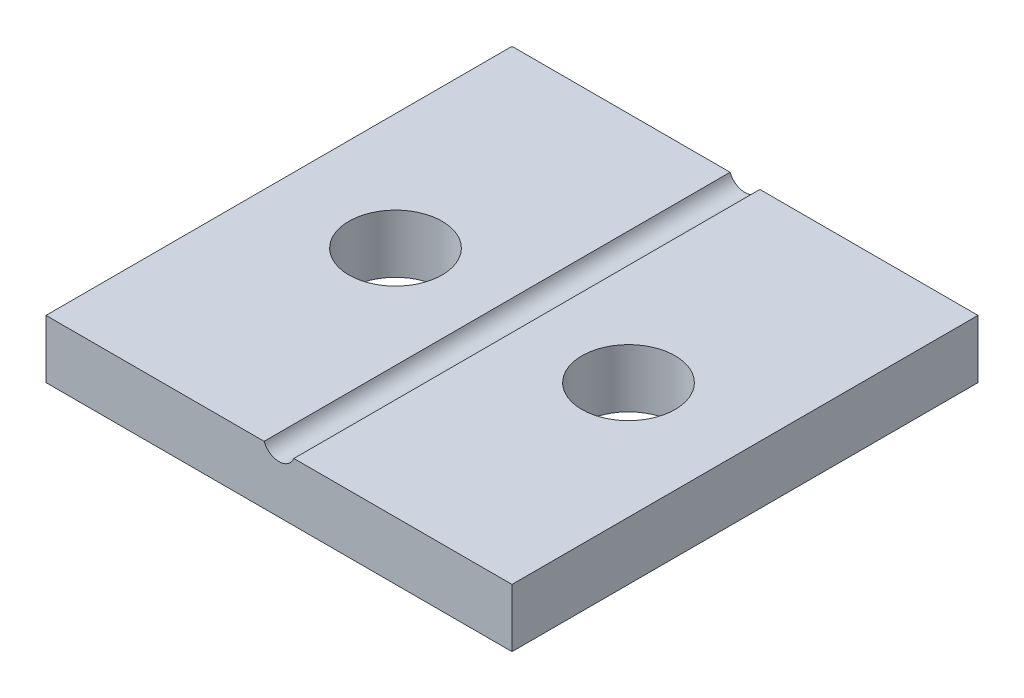
SolidWorks part; units mm, degrees
ref_plane "Front Plane" through (0, 0, 0) normal (0, 0, 1) x (1, 0, 0)
ref_plane "Top Plane" through (0, 0, 0) normal (0, 1, 0) x (1, 0, 0)
ref_plane "Right Plane" through (0, 0, 0) normal (1, 0, 0) x (0, 0, -1)
sketch "Sketch1" plane through (0, 0, 0) normal (0, 1, 0) x (1, 0, 0)
  line L1 (-60.7547, 52.0755) -> (-40.7547, 52.0755)
  line L2 (-60.7547, 52.0755) -> (-60.7547, 32.0755)
  line L3 (-60.7547, 32.0755) -> (-40.7547, 32.0755)
  line L4 (-40.7547, 52.0755) -> (-40.7547, 32.0755)
  dimension "D1" = 20
  dimension "D2" = 20
extrude "Boss-Extrude1" add sketch "Sketch1" along normal blind 2.5
sketch "Sketch2" plane through (0, 0, -32.0755) normal (0, 0, 1) x (1, 0, 0)
  line L0 (-60.7547, 2.5) -> (-40.7547, 2.5) construction
  line L1 (-50.7547, 6.7696) -> (-50.7547, 3.4135) construction
  circle A0 centre (-50.7547, 2.75) radius 0.6858
  point P6 (-50.7547, 2.5)
  dimension "D2" = 1.3716
  dimension "D1" = 0.25
extrude "Cut-Extrude1" cut sketch "Sketch2" against normal through all contours A0
sketch "Sketch3" plane through (0, 2.5, 0) normal (0, 1, 0) x (1, 0, 0)
  line L0 (-55.7547, 42.0755) -> (-45.7547, 42.0755) construction
  line L3 (-60.7547, 52.0755) -> (-40.7547, 32.0755) construction
  line L4 (-40.7547, 52.0755) -> (-60.7547, 32.0755) construction
  circle A0 centre (-55.7547, 42.0755) radius 2
  circle A1 centre (-45.7547, 42.0755) radius 2
  point P2 (-50.7547, 42.0755)
  dimension "D2" = 4
  dimension "D1" = 10
extrude "Cut-Extrude2" cut sketch "Sketch3" against normal through all
